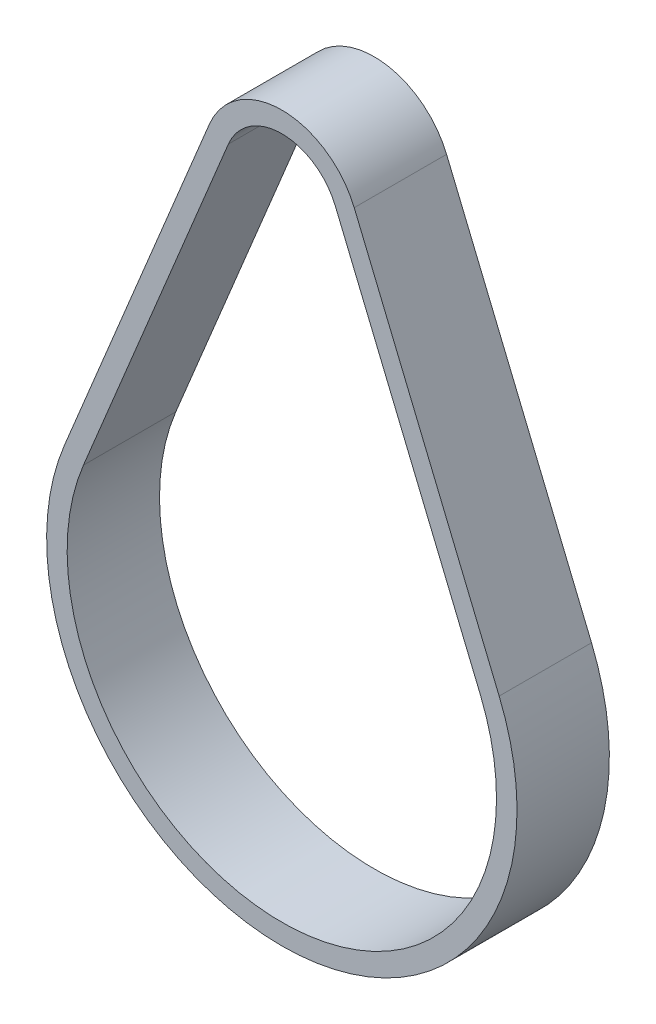
SolidWorks part; units mm, degrees
material "Rubber"
ref_plane "Front Plane" through (0, 0, 0) normal (0, 0, 1) x (1, 0, 0)
ref_plane "Top Plane" through (0, 0, 0) normal (0, 1, 0) x (1, 0, 0)
ref_plane "Right Plane" through (0, 0, 0) normal (1, 0, 0) x (0, 0, -1)
sketch "Sketch1" plane through (0, 0, 0) normal (0, 0, 1) x (1, 0, 0)
  line L0 (-7.0556, 2.9175) -> (-21.1806, -31.2417)
  line L1 (7.0556, 2.9175) -> (21.1806, -31.2417)
  arc A0 (7.0556, 2.9175) -> (-7.0556, 2.9175) centre (0, 0) ccw
  arc A1 (-21.1806, -31.2417) -> (21.1806, -31.2417) centre (0, -40) ccw
  dimension "D1" = 15.27
  dimension "D2" = 45.84
  dimension "D3" = 40
extrude "Extrude-Thin1" add sketch "Sketch1" along normal mid plane 9 thin thin type one direction reverse wall 2
